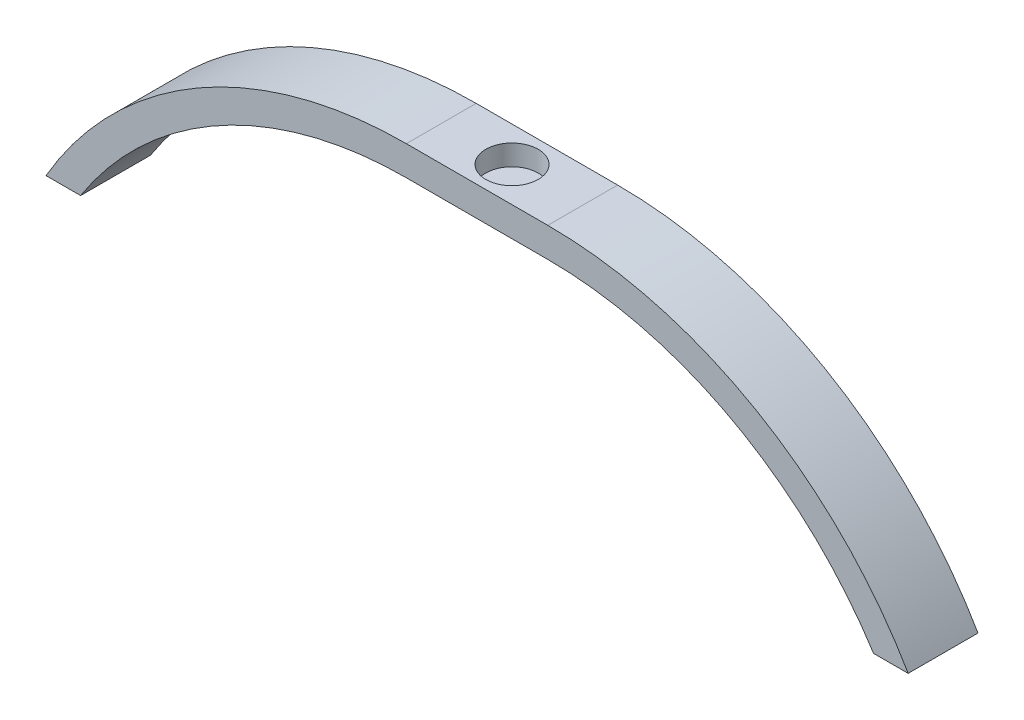
SolidWorks part; units mm, degrees
other "Markup1"
sketch "Sketch3"
material "6061 Alloy"
ref_plane "Front Plane" through (0, 0, 0) normal (0, 0, 1) x (1, 0, 0)
ref_plane "Top Plane" through (0, 0, 0) normal (0, 1, 0) x (1, 0, 0)
ref_plane "Right Plane" through (0, 0, 0) normal (1, 0, 0) x (0, 0, -1)
sketch "Sketch1" plane through (0, 0, 0) normal (0, 0, 1) x (1, 0, 0)
  line L0 (-10.2908, 0) -> (10.2908, 0) construction
  line L1 (-10.29, 60.57) -> (10.29, 60.57)
  line L3 (-62.72, 30.33) -> (62.72, 30.33) construction
  line L4 (-10.29, 56.27) -> (10.29, 56.27)
  line L5 (62.72, 30.33) -> (57.6871, 30.33)
  line L6 (-62.72, 30.33) -> (-57.6871, 30.33)
  arc A0 (-10.29, 60.57) -> (-62.72, 30.33) centre (-10.2908, 0) ccw
  arc A1 (62.72, 30.33) -> (10.29, 60.57) centre (10.2908, 0) ccw
  arc A2 (57.6871, 30.33) -> (10.29, 56.27) centre (10.2908, 0) ccw
  arc A3 (-10.29, 56.27) -> (-57.6871, 30.33) centre (-10.2908, 0) ccw
  arc A4 (-10.29, 56.27) -> (-58.9979, 28.1768) centre (-10.2908, 0) ccw construction
  arc A5 (58.9979, 28.1768) -> (10.29, 56.27) centre (10.2908, 0) ccw construction
  point P2 (0, 0)
  point P5 (0, 60.57)
  dimension "D3" = 20.58
  dimension "D1" = 60.57
  dimension "D2" = 125.44
  dimension "D4" = 30.24
  dimension "D5" = 4.3
extrude "Boss-Extrude1" add sketch "Sketch1" along normal blind 10.16
sketch "Sketch2" plane through (0, 60.57, 0) normal (0, 1, 0) x (1, 0, 0)
  circle A0 centre (0, -5.08) radius 3.81
  dimension "D1" = 7.62
extrude "Cut-Extrude1" cut sketch "Sketch2" against normal blind 3
